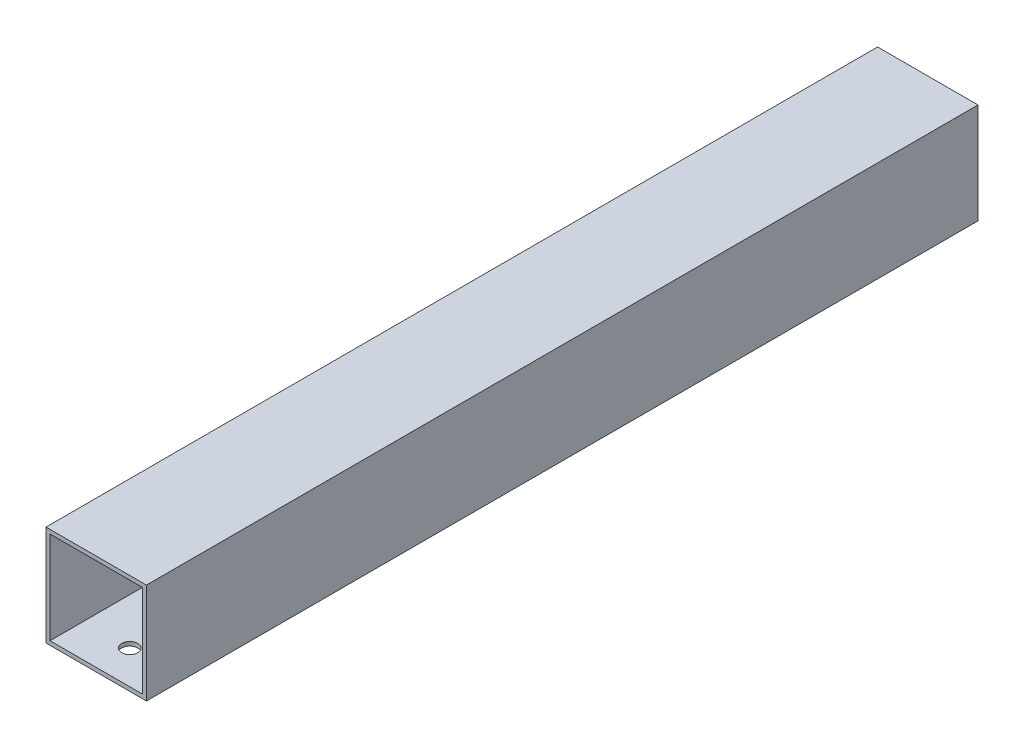
SolidWorks part; units mm, degrees
material "1023 Carbon Steel Sheet (SS)"
ref_plane "Plan de face" through (0, 0, 0) normal (0, 0, 1) x (1, 0, 0)
ref_plane "Plan de dessus" through (0, 0, 0) normal (0, 1, 0) x (1, 0, 0)
ref_plane "Plan de droite" through (0, 0, 0) normal (1, 0, 0) x (0, 0, -1)
sketch "Sketch1" plane through (0, 0, 0) normal (0, 0, 1) x (1, 0, 0)
  line L0 (2, -2) -> (-48, -2)
  line L1 (0, 0) -> (-46, 0)
  line L2 (0, 0) -> (0, 46)
  line L3 (0, 46) -> (-46, 46)
  line L4 (-46, 0) -> (-46, 46)
  line L5 (-48, -2) -> (-48, 48)
  line L6 (2, 48) -> (-48, 48)
  line L7 (2, -2) -> (2, 48)
  dimension "D1" = 50
  dimension "D2" = 50
  dimension "D3" = 2
extrude "steelTube" add sketch "Sketch1" along normal blind 414
sketch "Sketch2" plane through (0, -2, 0) normal (0, -1, 0) x (1, 0, 0)
  line L0 (-48, 0) -> (2, 0) construction
  line L3 (-48, 414) -> (2, 414) construction
  line L4 (2, 30.3284) -> (2, 417.3284) construction
  circle A0 centre (-23, 50.3) radius 4
  circle A1 centre (-23, 397.3) radius 4
  dimension "D2" = 8
  dimension "D4" = 8
  dimension "D1" = 50.3
  dimension "D3" = 25
  dimension "D5" = 16.7
  dimension "D6" = 25
extrude "Cut-Extrude1" cut sketch "Sketch2" against normal blind 2
